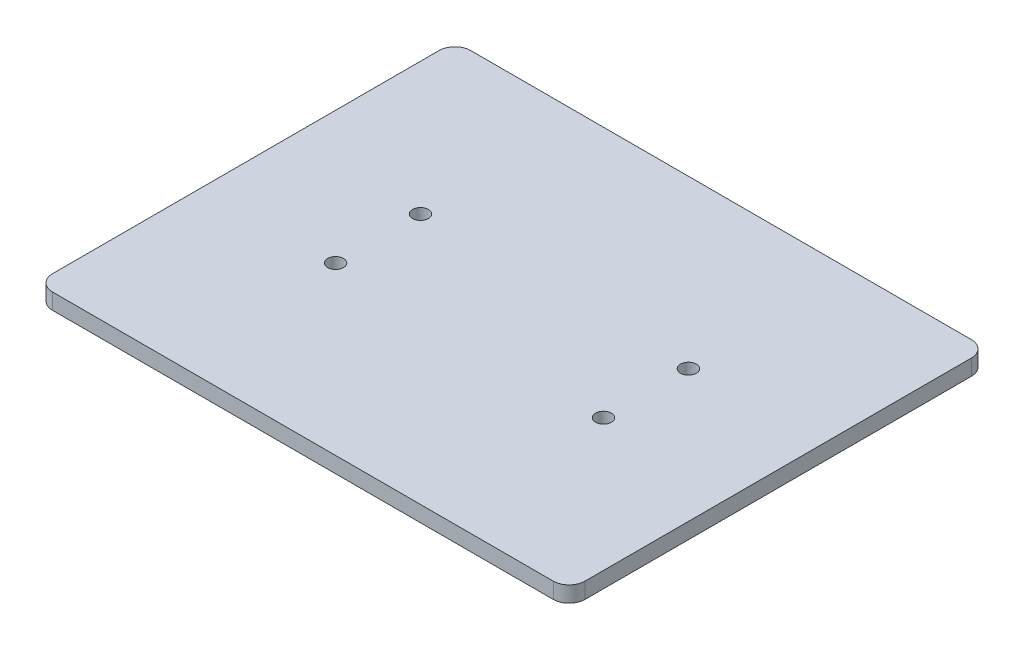
SolidWorks part; units mm, degrees
ref_plane "Спереди" through (0, 0, 0) normal (0, 0, 1) x (1, 0, 0)
ref_plane "Сверху" through (0, 0, 0) normal (0, 1, 0) x (1, 0, 0)
ref_plane "Справа" through (0, 0, 0) normal (1, 0, 0) x (0, 0, -1)
sketch "Эскиз1" plane through (0, 0, 0) normal (0, 1, 0) x (1, 0, 0)
  line L0 (0, 0) -> (167.75, 0)
  line L1 (0, 0) -> (0, 131.75)
  line L2 (0, 131.75) -> (167.75, 131.75)
  line L3 (167.75, 131.75) -> (167.75, 0)
  dimension "D1" = 167.75
  dimension "D2" = 131.75
  dimension "D3" = 167.75
extrude "Бобышка-Вытянуть1" add sketch "Эскиз1" along normal blind 5
fillet "Скругление1" radius 5 1 edges at (0, 2.5, 0)
fillet "Скругление2" radius 5 1 edges at (0, 2.5, -131.75)
fillet "Скругление3" radius 5 1 edges at (167.75, 2.5, -131.75)
fillet "Скругление4" radius 5 1 edges at (167.75, 2.5, 0)
sketch "Эскиз2" plane through (0, 5, 0) normal (0, 1, 0) x (1, 0, 0)
  line L0 (167.75, 65.875) -> (0, 65.875) construction
  line L1 (167.75, 5) -> (167.75, 126.75) construction
  line L2 (0, 126.75) -> (0, 5) construction
  line L3 (83.875, 0) -> (83.875, 131.75) construction
  line L4 (5, 0) -> (162.75, 0) construction
  line L5 (162.75, 131.75) -> (5, 131.75) construction
  line L6 (83.875, 65.875) -> (31.675, 65.875)
  line L7 (83.875, 65.875) -> (136.075, 65.875)
  line L8 (136.075, 101.75) -> (136.075, 30)
  line L9 (31.675, 101.75) -> (31.675, 30)
  line L10 (136.075, 30) -> (31.675, 30)
  line L11 (136.075, 101.75) -> (31.675, 101.75)
  line L12 (136.075, 101.75) -> (136.075, 79.255)
  circle A0 centre (126.075, 79.25) radius 2.5
  circle A1 centre (126.075, 52.5) radius 2.5
  circle A2 centre (41.675, 79.25) radius 2.5
  circle A3 centre (41.675, 52.5) radius 2.5
  dimension "D3" = 5
  dimension "D5" = 22.5
  dimension "D1" = 104.4
  dimension "D2" = 71.75
  dimension "D4" = 10
  dimension "D6" = 84.4
  dimension "D7" = 26.75
extrude "Вырез-Вытянуть1" cut sketch "Эскиз2" against normal blind 10 contours A2 | A3 | A0 | A1
